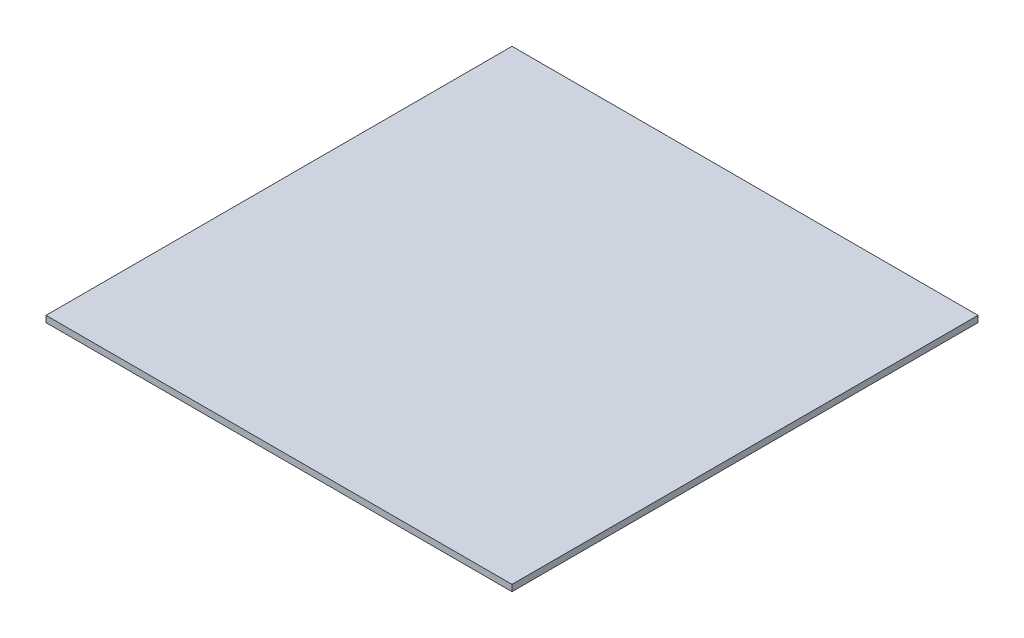
SolidWorks part; units mm, degrees
ref_plane "Front Plane" through (0, 0, 0) normal (0, 0, 1) x (1, 0, 0)
ref_plane "Top Plane" through (0, 0, 0) normal (0, 1, 0) x (1, 0, 0)
ref_plane "Right Plane" through (0, 0, 0) normal (1, 0, 0) x (0, 0, -1)
sketch "Sketch1" plane through (0, 0, 0) normal (0, 1, 0) x (1, 0, 0)
  line L1 (-121.2444, 138.7416) -> (98.7556, 138.7416)
  line L2 (-121.2444, 138.7416) -> (-121.2444, -81.2584)
  line L3 (-121.2444, -81.2584) -> (98.7556, -81.2584)
  line L4 (98.7556, 138.7416) -> (98.7556, -81.2584)
  dimension "D1" = 220
  dimension "D2" = 220
extrude "Boss-Extrude1" add sketch "Sketch1" along normal blind 3
